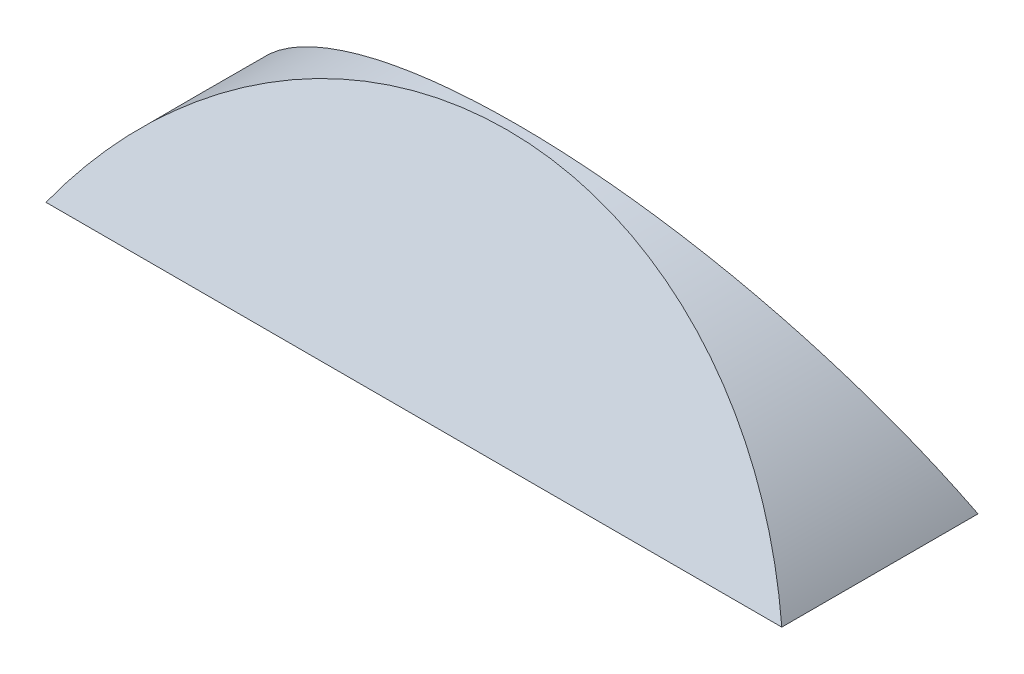
SolidWorks part; units mm, degrees
ref_plane "Ebene vorne" through (0, 0, 0) normal (0, 0, 1) x (1, 0, 0)
ref_plane "Ebene oben" through (0, 0, 0) normal (0, 1, 0) x (1, 0, 0)
ref_plane "Ebene rechts" through (0, 0, 0) normal (1, 0, 0) x (0, 0, -1)
sketch "Skizze1" plane through (0, 0, 0) normal (0, 1, 0) x (1, 0, 0)
  line L1 (-75, -20) -> (75, -20)
  line L2 (-75, -20) -> (-75, 20)
  line L3 (-75, 20) -> (75, 20)
  line L4 (75, -20) -> (75, 20)
  line L5 (-75, -20) -> (75, 20) construction
  line L6 (-75, 20) -> (75, -20) construction
  point P0 (0, 0)
  dimension "D1" = 40
  dimension "D2" = 150
ref_plane "Ebene1" through (0, 7.6604, 16.4279) normal (0, 0.4226, 0.9063) x (1, 0, 0)
ref_plane "Ebene2" through (0, 7.6604, -16.4279) normal (0, -0.4226, 0.9063) x (1, 0, 0)
sketch "Skizze2" plane through (0, 7.6604, 16.4279) normal (0, 0.4226, 0.9063) x (1, 0, 0)
  line L0 (-75, -8.4524) -> (75, -8.4524) construction
  line L1 (-75, -8.4524) -> (75, -8.4524)
  arc A0 (-75, -8.4524) -> (75, -8.4524) centre (0, -48.4524) cw
  dimension "D1" = 45
sketch "Skizze3" plane through (0, 7.6604, -16.4279) normal (0, -0.4226, 0.9063) x (1, 0, 0)
  line L0 (-75, -8.4524) -> (75, -8.4524) construction
  line L1 (-75, -8.4524) -> (75, -8.4524)
  arc A0 (75, -8.4524) -> (-75, -8.4524) centre (0, -48.4524) ccw
  dimension "D1" = 45
loft "Ausformung1" add profiles "Skizze2", "Skizze3"
